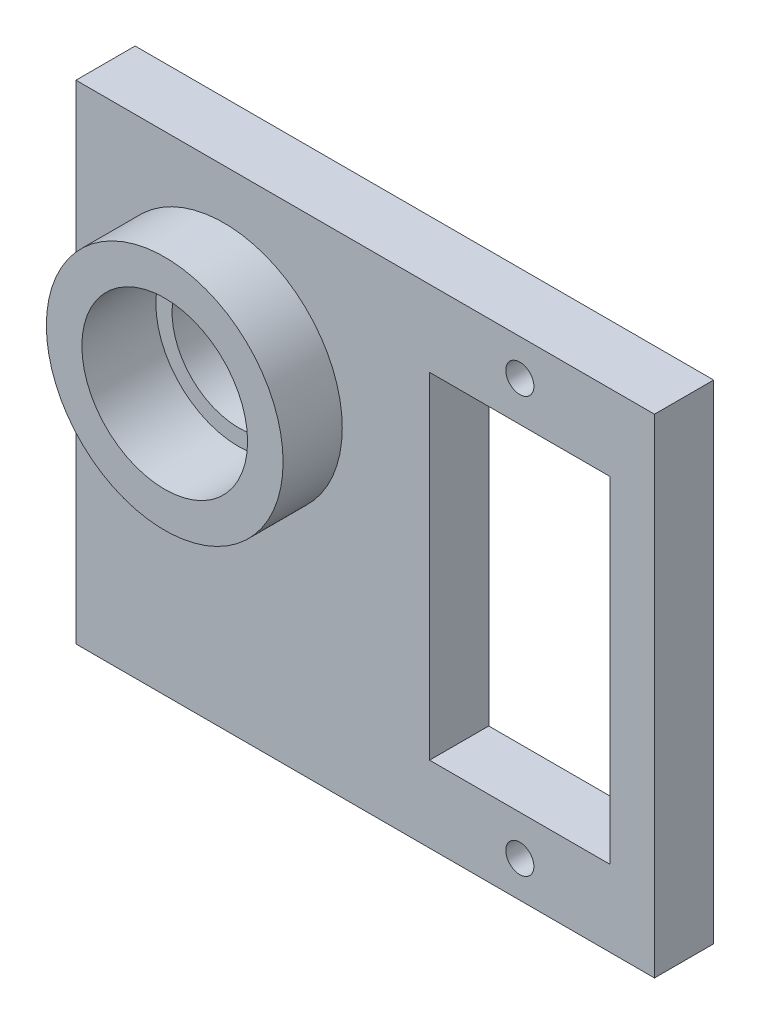
SolidWorks part; units mm, degrees
ref_plane "Front Plane" through (0, 0, 0) normal (0, 0, 1) x (1, 0, 0)
ref_plane "Top Plane" through (0, 0, 0) normal (0, 1, 0) x (1, 0, 0)
ref_plane "Right Plane" through (0, 0, 0) normal (1, 0, 0) x (0, 0, -1)
sketch "Sketch1" plane through (0, 0, 0) normal (0, 0, 1) x (1, 0, 0)
  line L0 (0, 6.2) -> (0, -16.5) construction
  line L1 (-6.1, 6.2) -> (6.1, 6.2)
  line L2 (-6.1, 6.2) -> (-6.1, -16.5)
  line L3 (-6.1, -16.5) -> (6.1, -16.5)
  line L4 (6.1, -16.5) -> (6.1, 6.2)
  line L5 (9.1, -21.65) -> (9.1, 11.35)
  line L6 (9.1, 11.35) -> (-30, 11.35)
  line L7 (-30, 11.35) -> (-30, -21.65)
  line L8 (-30, -21.65) -> (9.1, -21.65)
  circle A0 centre (0, 8.9) radius 0.95
  circle A1 centre (0, -19.2) radius 0.95
  circle A2 centre (-20, 0) radius 4.5
  point P11 (0, 6.2)
  point P16 (9.1, -5.15)
  point P17 (6.1, -5.15)
  dimension "D3" = 1.9
  dimension "D11" = 9
  dimension "D1" = 8.9
  dimension "D2" = 19.2
  dimension "D4" = 22.7
  dimension "D5" = 2.7
  dimension "D6" = 2.7
  dimension "D7" = 12.2
  dimension "D8" = 3
  dimension "D9" = 33
  dimension "D10" = 20
  dimension "D12" = 10
extrude "Boss-Extrude1" add sketch "Sketch1" along normal blind 4
sketch "Sketch2" plane through (0, 0, 0) normal (0, 0, 1) x (1, 0, 0)
  circle A0 centre (-20, 0) radius 4.4038
  circle A1 centre (-20, 0) radius 8
  dimension "D1" = 16
extrude "Boss-Extrude2" add sketch "Sketch2" along normal blind 4 from surface at 4 starting at face at (0, -5.15, 4)
sketch "Sketch3" plane through (0, 0, 0) normal (0, 0, 1) x (1, 0, 0)
  circle A0 centre (-20, 0) radius 5.6
  dimension "D1" = 11.2
extrude "Cut-Extrude1" cut sketch "Sketch3" against normal blind 5 from surface at 8 starting at face at (-12, 0, 8)
